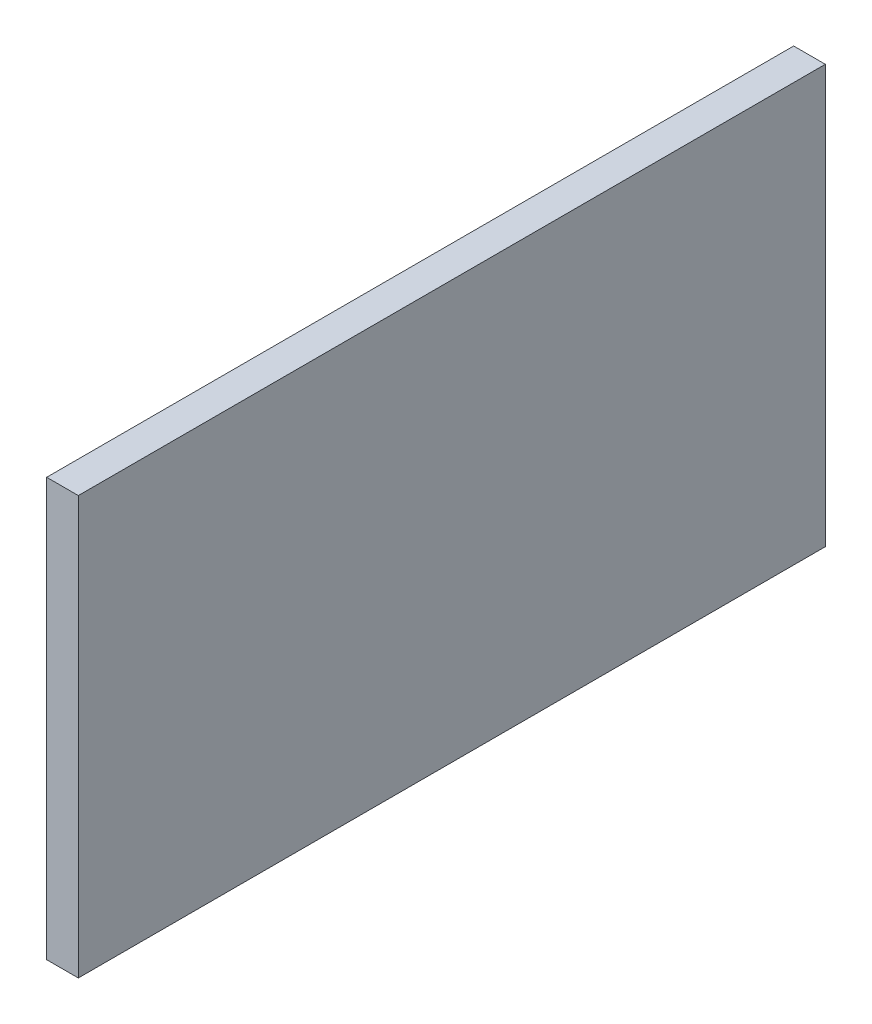
SolidWorks part; units mm, degrees
material "POLYURETHANE (11671)"
ref_plane "Front Plane" through (0, 0, 0) normal (0, 0, 1) x (1, 0, 0)
ref_plane "Top Plane" through (0, 0, 0) normal (0, 1, 0) x (1, 0, 0)
ref_plane "Right Plane" through (0, 0, 0) normal (1, 0, 0) x (0, 0, -1)
sketch "Sketch1" plane through (0, 0, 0) normal (1, 0, 0) x (0, 0, -1)
  line L1 (-37.465, -20.955) -> (37.465, -20.955)
  line L2 (-37.465, -20.955) -> (-37.465, 20.955)
  line L3 (-37.465, 20.955) -> (37.465, 20.955)
  line L4 (37.465, -20.955) -> (37.465, 20.955)
  line L5 (-37.465, -20.955) -> (37.465, 20.955) construction
  line L6 (-37.465, 20.955) -> (37.465, -20.955) construction
  point P0 (0, 0)
  dimension "D1" = 74.93
  dimension "D2" = 41.91
extrude "Boss-Extrude1" add sketch "Sketch1" along normal blind 3.175
